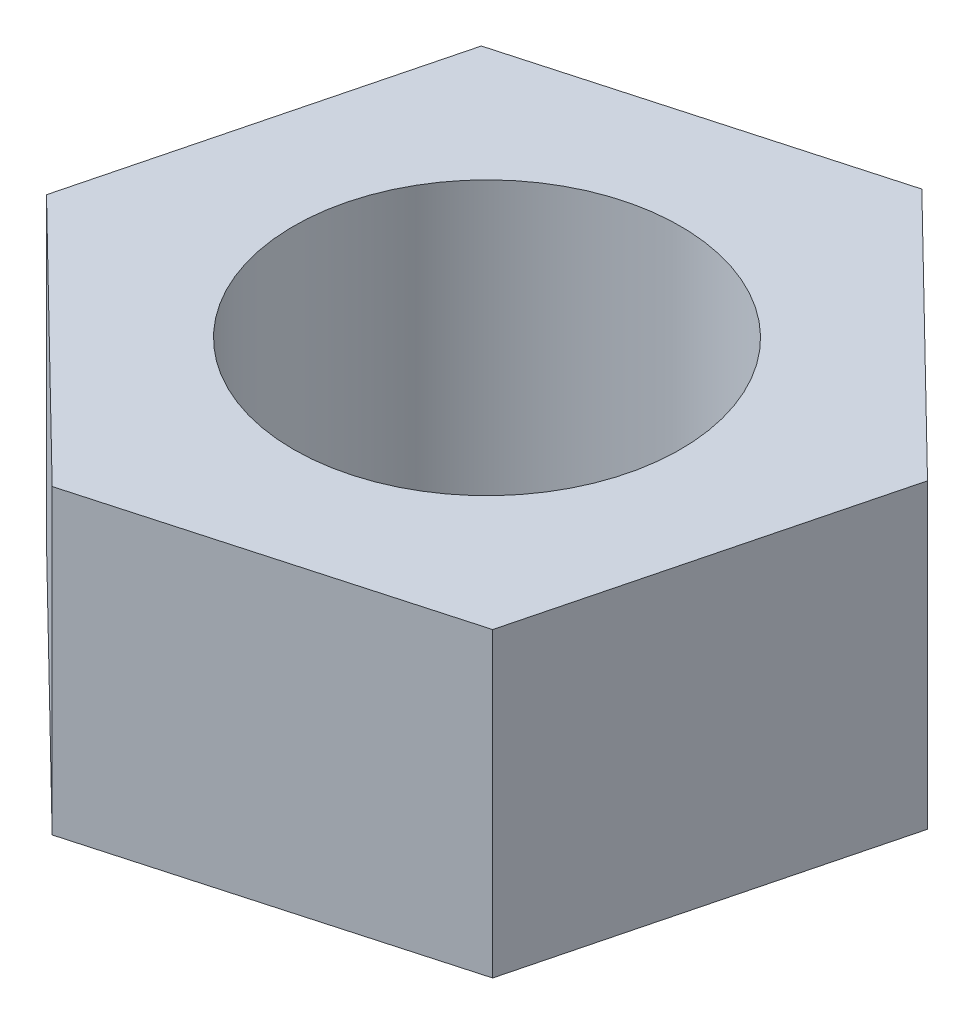
SolidWorks part; units mm, degrees
ref_plane "前视基准面" through (0, 0, 0) normal (0, 0, 1) x (1, 0, 0)
ref_plane "上视基准面" through (0, 0, 0) normal (0, 1, 0) x (1, 0, 0)
ref_plane "右视基准面" through (0, 0, 0) normal (1, 0, 0) x (0, 0, -1)
sketch "草图1" plane through (0, 0, 0) normal (0, 1, 0) x (1, 0, 0)
  line L1 (3.3025, -3.2291) -> (4.4477, 1.2455)
  line L2 (4.4477, 1.2455) -> (1.1452, 4.4746)
  line L3 (1.1452, 4.4746) -> (-3.3025, 3.2291)
  line L4 (-3.3025, 3.2291) -> (-4.4477, -1.2455)
  line L5 (-4.4477, -1.2455) -> (-1.1452, -4.4746)
  line L6 (-1.1452, -4.4746) -> (3.3025, -3.2291)
  circle A0 centre (0, 0) radius 2.5
  circle A1 centre (0, 0) radius 4 construction
  dimension "D1" = 5
  dimension "D2" = 8
extrude "凸台-拉伸1" add sketch "草图1" along normal blind 3.9
